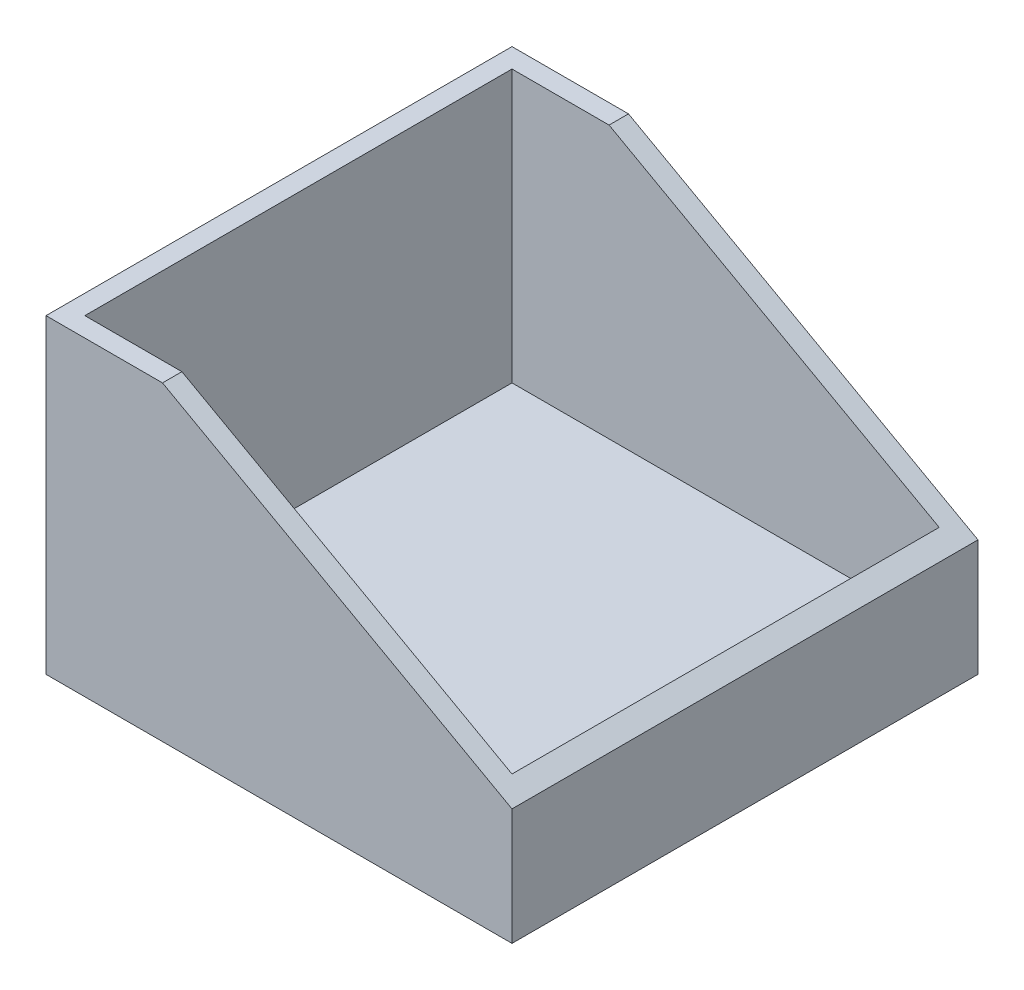
SolidWorks part; units mm, degrees
ref_plane "Front Plane" through (0, 0, 0) normal (0, 0, 1) x (1, 0, 0)
ref_plane "Top Plane" through (0, 0, 0) normal (0, 1, 0) x (1, 0, 0)
ref_plane "Right Plane" through (0, 0, 0) normal (1, 0, 0) x (0, 0, -1)
sketch "Sketch1" plane through (0, 0, 0) normal (0, 0, 1) x (1, 0, 0)
  line L0 (0, 0) -> (0, 101.6)
  line L1 (0, 101.6) -> (152.4, 101.6)
  line L2 (152.4, 101.6) -> (152.4, 0)
  line L3 (152.4, 0) -> (0, 0)
  dimension "D1" = 101.6
  dimension "D2" = 152.4
extrude "Boss-Extrude1" add sketch "Sketch1" along normal blind 152.4
sketch "Sketch6" plane through (0, 0, 152.4) normal (0, 0, 1) x (1, 0, 0)
  line L0 (38.1, 101.6) -> (152.4, 101.6)
  line L1 (152.4, 101.6) -> (0, 101.6) construction
  line L2 (152.4, 101.6) -> (152.4, 38.1)
  line L3 (152.4, 0) -> (152.4, 101.6) construction
  line L4 (152.4, 38.1) -> (38.1, 101.6)
  line L5 (104.4367, 101.6) -> (104.5902, 101.6)
  line M5 (152.4, 0) -> (152.4, 101.6)
  line M6 (152.4, 101.6) -> (0, 101.6)
  dimension "D1" = 63.5
  dimension "D2" = 114.3
extrude "Cut-Extrude2" cut sketch "Sketch6" against normal blind 152.4 contours L4 L0 M5 M6
sketch "Sketch7" plane through (0, 101.6, 0) normal (0, 1, 0) x (1, 0, 0)
  line L0 (6.35, -6.35) -> (6.35, -146.05)
  line L1 (6.35, -146.05) -> (146.05, -146.05)
  line L2 (146.05, -146.05) -> (146.05, -6.35)
  line L3 (146.05, -6.35) -> (6.35, -6.35)
  line L4 (38.1, 0) -> (0, 0) construction
  line L5 (0, -152.4) -> (0, 0) construction
  line L6 (152.4, -152.4) -> (38.1, -152.4) construction
  line L7 (152.4, 0) -> (152.4, -152.4) construction
  dimension "D1" = 6.35
  dimension "D2" = 6.35
  dimension "D3" = 6.35
  dimension "D4" = 6.35
extrude "Cut-Extrude3" cut sketch "Sketch7" against normal blind 88.9
